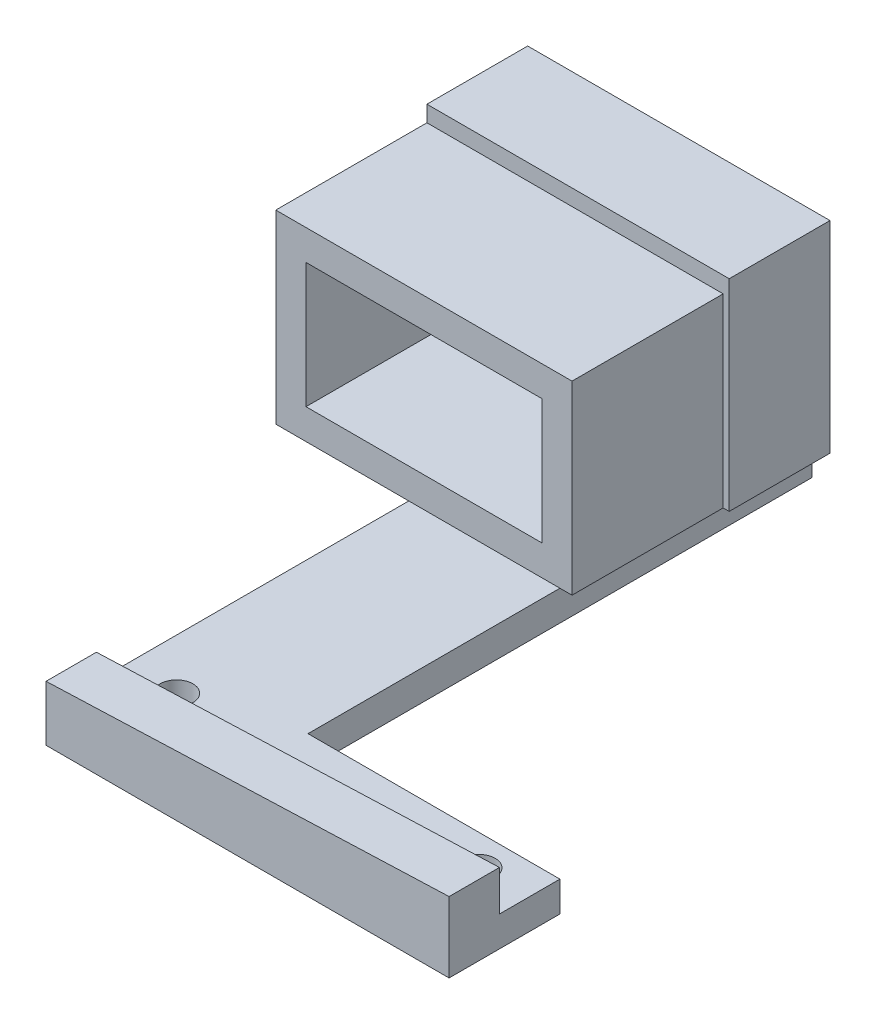
SolidWorks part; units mm, degrees
ref_plane "Plan de face" through (0, 0, 0) normal (0, 0, 1) x (1, 0, 0)
ref_plane "Plan de dessus" through (0, 0, 0) normal (0, 1, 0) x (1, 0, 0)
ref_plane "Plan de droite" through (0, 0, 0) normal (1, 0, 0) x (0, 0, -1)
sketch "Esquisse1" plane through (0, 0, 0) normal (0, 0, 1) x (1, 0, 0)
  line L1 (0, 0) -> (40, 0)
  line L2 (0, 0) -> (0, -7)
  line L3 (0, -7) -> (40, -7)
  line L4 (40, 0) -> (40, -7)
  dimension "D1" = 40
  dimension "D2" = 7
extrude "Boss.-Extru.1" add sketch "Esquisse1" along normal blind 5
sketch "Esquisse3" plane through (0, 0, 5) normal (0, 0, 1) x (1, 0, 0)
  line L0 (40, 0) -> (0, 0)
  line L1 (0, 0) -> (0, -1.5)
  line L3 (0, -1.5) -> (40, 0)
  dimension "D1" = 1.5
extrude "Enlèv. mat.-Extru.2" cut sketch "Esquisse3" against normal through all
sketch "Esquisse4" plane through (0, 0, 0) normal (0, 0, -1) x (-1, 0, 0)
  line L0 (-40, -7) -> (-40, 0) construction
  line L1 (0, -7) -> (-40, -7)
  line L2 (0, -7) -> (0, -4)
  line L3 (0, -4) -> (-40, -4)
  line L4 (-40, -7) -> (-40, -4)
  dimension "D1" = 3
extrude "Boss.-Extru.2" add sketch "Esquisse4" along normal blind 6
sketch "Esquisse5" plane through (0, -4, 0) normal (0, 1, 0) x (1, 0, 0)
  line L0 (0, 6) -> (0, 0) construction
  circle A0 centre (35, 2.9497) radius 1.625
  circle A1 centre (5, 2.9497) radius 1.625
  dimension "D1" = 3.25
  dimension "D2" = 3.25
  dimension "D3" = 30
  dimension "D4" = 5
extrude "Enlèv. mat.-Extru.3" cut sketch "Esquisse5" against normal blind 6
sketch "Esquisse6" plane through (0, 0, -6) normal (0, 0, -1) x (-1, 0, 0)
  line L0 (0, -4) -> (-40, -4) construction
  line L1 (-15, -4) -> (0, -4)
  line L2 (-15, -4) -> (-15, -7)
  line L3 (-15, -7) -> (0, -7)
  line L4 (0, -4) -> (0, -7)
  dimension "D1" = 15
extrude "Boss.-Extru.3" add sketch "Esquisse6" along normal blind 50
sketch "Esquisse7" plane through (0, 0, 0) normal (-1, 0, 0) x (0, 0, 1)
  line L0 (5, -7) -> (-56, -7) construction
  line L1 (-56, -4) -> (-46, -4)
  line L2 (-56, -4) -> (-56, -7)
  line L3 (-56, -7) -> (-46, -7)
  line L4 (-46, -4) -> (-46, -7)
  dimension "D1" = 10
extrude "Boss.-Extru.4" add sketch "Esquisse7" along normal blind 13.2
sketch "Esquisse8" plane through (0, -4, 0) normal (0, 1, 0) x (1, 0, 0)
  line L0 (-13.2, 56) -> (15, 56) construction
  line L1 (-13.2, 46) -> (16.8, 46)
  line L2 (-13.2, 46) -> (-13.2, 56)
  line L3 (-13.2, 56) -> (16.8, 56)
  line L4 (16.8, 46) -> (16.8, 56)
  dimension "D1" = 30
extrude "Boss.-Extru.5" add sketch "Esquisse8" along normal blind 20
sketch "Esquisse9" plane through (0, 0, -46) normal (0, 0, 1) x (1, 0, 0)
  line L0 (-13.2, -7) -> (-13.2, 16) construction
  line L1 (13.2, 11.4) -> (-10.2, 11.4)
  line L2 (13.2, 11.4) -> (13.2, -1)
  line L3 (13.2, -1) -> (-10.2, -1)
  line L4 (-10.2, 11.4) -> (-10.2, -1)
  line L5 (16.2, 14.4) -> (-13.2, 14.4)
  line L6 (16.2, 14.4) -> (16.2, -4)
  line L7 (16.2, -4) -> (-13.2, -4)
  line L8 (-13.2, 14.4) -> (-13.2, -4)
  line L9 (-13.2, -7) -> (0, -7) construction
  dimension "D1" = 3
  dimension "D2" = 3
  dimension "D3" = 3
  dimension "D4" = 3
  dimension "D5" = 0
  dimension "D6" = 3
  dimension "D7" = 23.4
  dimension "D8" = 12.4
extrude "Boss.-Extru.6" add sketch "Esquisse9" along normal blind 15
sketch "Esquisse11" plane through (0, 0, -56) normal (0, 0, -1) x (-1, 0, 0)
  line L0 (13.2, 16) -> (13.2, -7) construction
  line L1 (13.2, 8) -> (3.2, 8)
  line L2 (13.2, 8) -> (13.2, 3)
  line L3 (13.2, 3) -> (3.2, 3)
  line L4 (3.2, 8) -> (3.2, 3)
  line L5 (-15, -7) -> (13.2, -7) construction
  dimension "D1" = 5
  dimension "D2" = 10
  dimension "D3" = 10
extrude "Enlèv. mat.-Extru.5" cut sketch "Esquisse11" against normal blind 15
